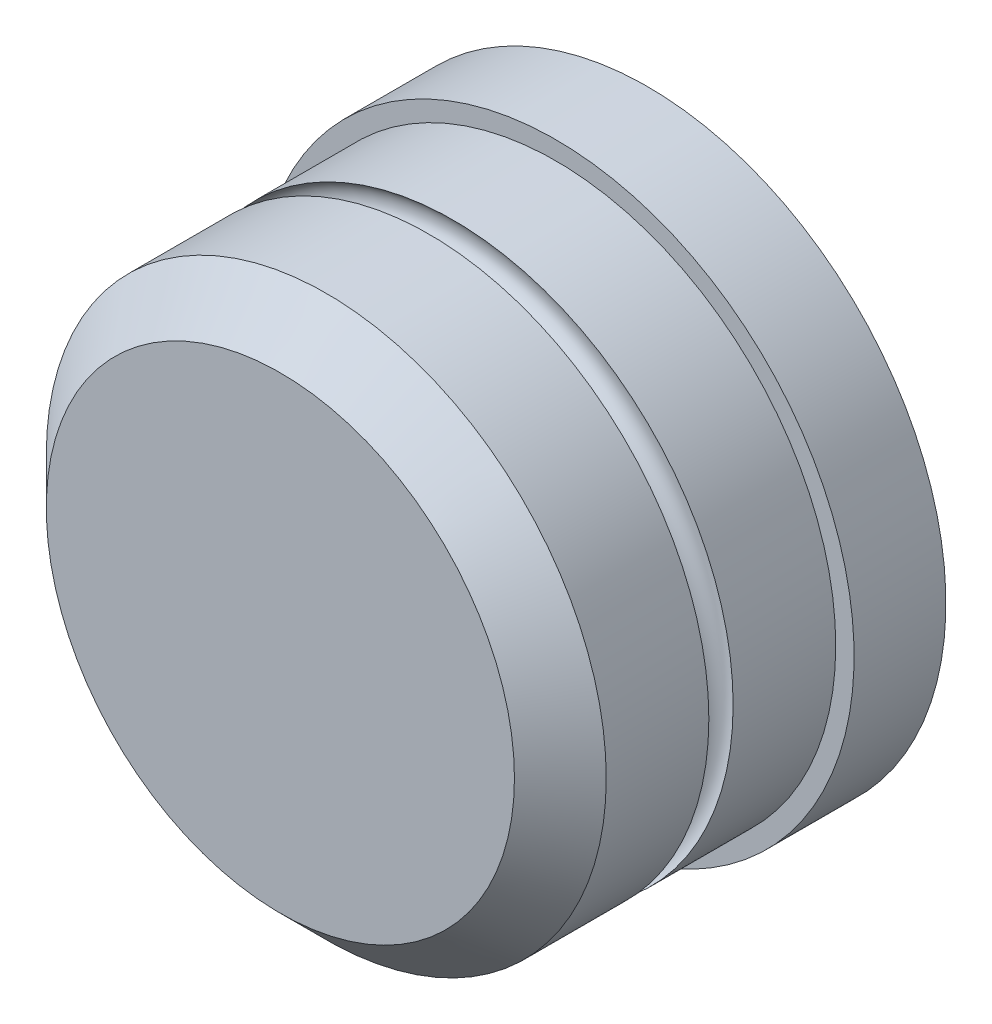
SolidWorks part; units mm, degrees
ref_plane "Plan de face" through (0, 0, 0) normal (0, 0, 1) x (1, 0, 0)
ref_plane "Plan de dessus" through (0, 0, 0) normal (0, 1, 0) x (1, 0, 0)
ref_plane "Plan de droite" through (0, 0, 0) normal (1, 0, 0) x (0, 0, -1)
sketch "Esquisse1" plane through (0, 0, 0) normal (0, 0, 1) x (1, 0, 0)
  circle A0 centre (0, 0) radius 30.5
extrude "Boss.-Extru.1" add sketch "Esquisse1" along normal blind 30
sketch "Esquisse2" plane through (0, 0, 0) normal (0, 0, -1) x (-1, 0, 0)
  circle A0 centre (0, 0) radius 32.5
extrude "Boss.-Extru.2" add sketch "Esquisse2" along normal blind 10
chamfer "Chanfrein1" distance 5 angle 45 1 edges at (30.5, 0, 30)
sketch "Esquisse6" plane through (0, 0, 0) normal (0, 1, 0) x (1, 0, 0)
  circle A0 centre (-29, -12.5) radius 2
  point P6 (-28.8854, -12.5)
ref_plane "Plan2" through (0, 0, 10) normal (0, 0, 1) x (1, 0, 0)
sketch "Esquisse7" plane through (0, 0, 10) normal (0, 0, 1) x (1, 0, 0)
  circle A0 centre (0, 0) radius 26.0041
sweep "Enlèvement de matière-Balayage1" cut profiles "Esquisse6" path "Esquisse7"
